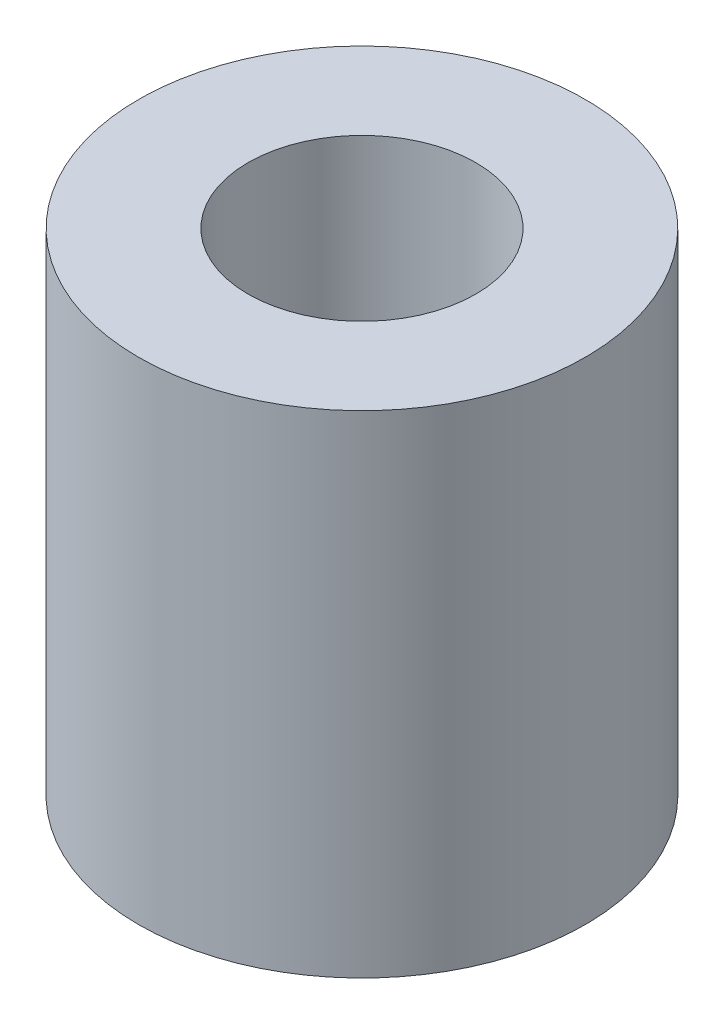
SolidWorks part; units mm, degrees
ref_plane "Plan de face" through (0, 0, 0) normal (0, 0, 1) x (1, 0, 0)
ref_plane "Plan de dessus" through (0, 0, 0) normal (0, 1, 0) x (1, 0, 0)
ref_plane "Plan de droite" through (0, 0, 0) normal (1, 0, 0) x (0, 0, -1)
sketch "Esquisse1" plane through (0, 0, 0) normal (0, 1, 0) x (1, 0, 0)
  circle A0 centre (0, 0) radius 5
  circle A1 centre (0, 0) radius 2.55
  dimension "D1" = 5.1
  dimension "D2" = 10
extrude "Boss.-Extru.1" add sketch "Esquisse1" along normal blind 11
